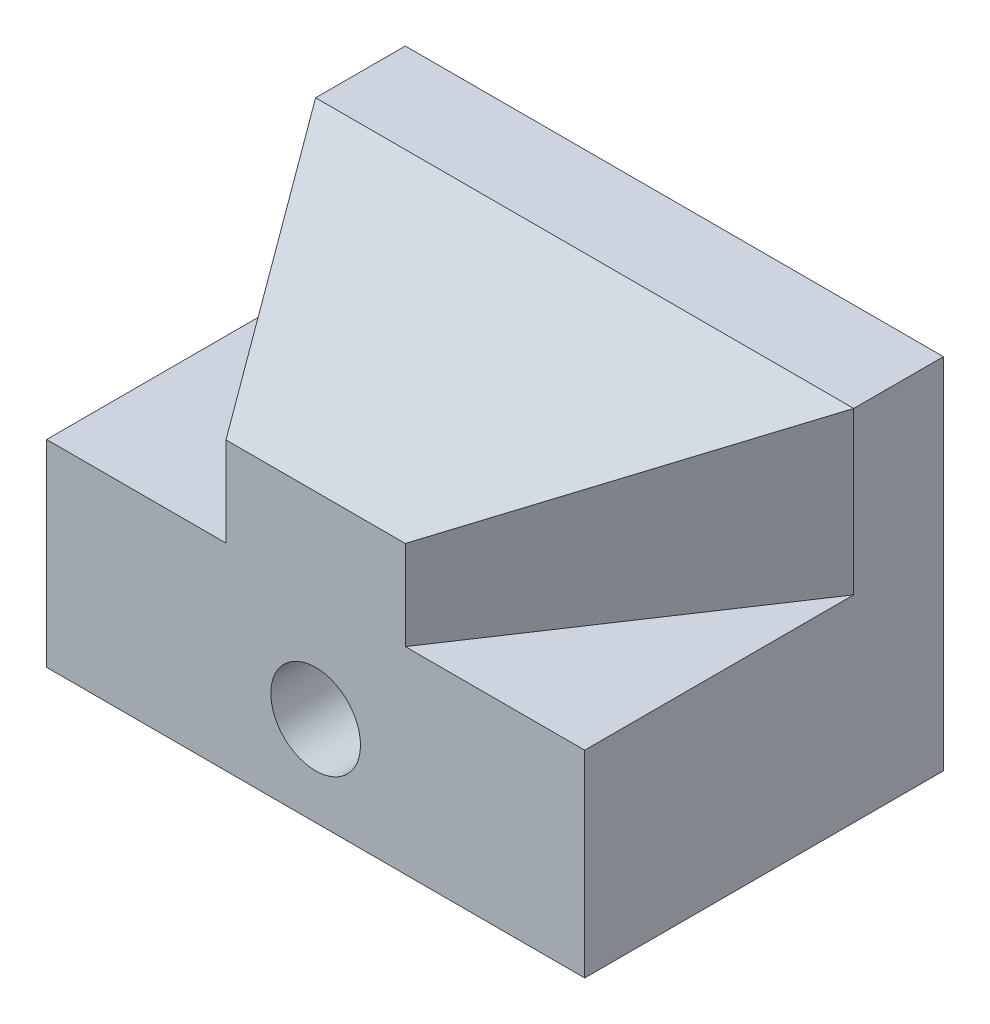
SolidWorks part; units mm, degrees
material "1060 Alloy"
ref_plane "Front Plane" through (0, 0, 0) normal (0, 0, 1) x (1, 0, 0)
ref_plane "Top Plane" through (0, 0, 0) normal (0, 1, 0) x (1, 0, 0)
ref_plane "Right Plane" through (0, 0, 0) normal (1, 0, 0) x (0, 0, -1)
sketch "Sketch1" plane through (0, 0, 0) normal (0, 0, 1) x (1, 0, 0)
  line L1 (0, 0) -> (76.2, 0)
  line L2 (0, 0) -> (0, 50.8)
  line L3 (0, 50.8) -> (76.2, 50.8)
  line L4 (76.2, 0) -> (76.2, 50.8)
  dimension "D1" = 76.2
  dimension "D2" = 50.8
extrude "Boss-Extrude1" add sketch "Sketch1" along normal blind 50.8
sketch "Sketch2" plane through (0, 50.8, 0) normal (0, 1, 0) x (1, 0, 0)
  line L0 (76.2, -12.7) -> (50.8, -50.8)
  line L1 (76.2, -50.8) -> (76.2, 0) construction
  line L2 (76.2, -50.8) -> (0, -50.8) construction
  line L3 (50.8, -50.8) -> (76.2, -50.8)
  line L4 (76.2, -50.8) -> (76.2, -12.7)
  line L5 (0, -12.7) -> (0, -50.8)
  line L6 (0, -50.8) -> (0, 0) construction
  line L7 (0, -50.8) -> (25.4, -50.8)
  line L8 (25.4, -50.8) -> (0, -12.7)
  dimension "D1" = 38.1
  dimension "D2" = 25.4
extrude "Cut-Extrude1" cut sketch "Sketch2" against normal blind 22.86 and the other way through all
sketch "Sketch3" plane through (76.2, 0, 0) normal (1, 0, 0) x (0, 0, -1)
  line L0 (-12.7, 50.8) -> (-50.8, 40.5911)
  line L1 (-50.8, 50.8) -> (-50.8, 27.94) construction
  line L2 (-50.8, 40.5911) -> (-50.8, 50.8)
  line L3 (-50.8, 50.8) -> (-12.7, 50.8)
  dimension "D1" = 15
extrude "Cut-Extrude2" cut sketch "Sketch3" against normal through all
sketch "Sketch6" plane through (0, 0, 50.8) normal (0, 0, 1) x (1, 0, 0)
  line L0 (76.2, 0) -> (76.2, 27.94) construction
  line L1 (0, 0) -> (76.2, 0) construction
  circle A0 centre (38.1, 12.7) radius 6.35
  dimension "D3" = 6.35
  dimension "D1" = 38.1
  dimension "D2" = 12.7
extrude "Cut-Extrude3" cut sketch "Sketch6" against normal through all
